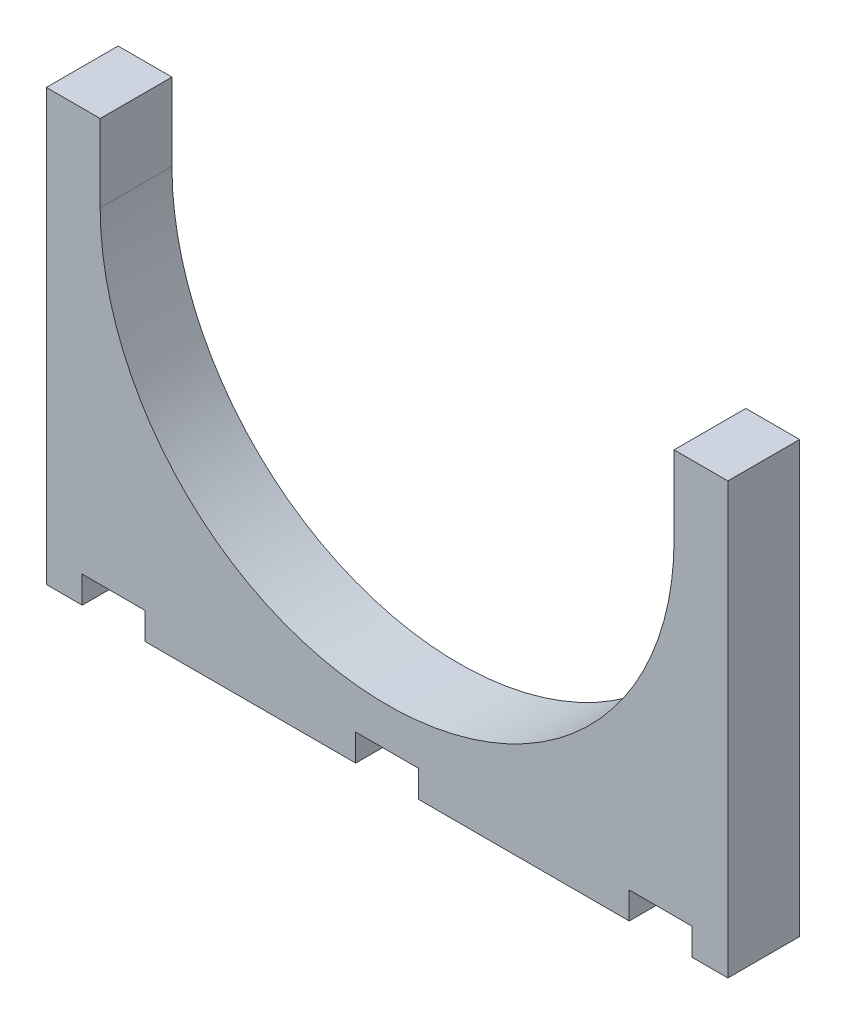
SolidWorks part; units mm, degrees
ref_plane "Front Plane" through (0, 0, 0) normal (0, 0, 1) x (1, 0, 0)
ref_plane "Top Plane" through (0, 0, 0) normal (0, 1, 0) x (1, 0, 0)
ref_plane "Right Plane" through (0, 0, 0) normal (1, 0, 0) x (0, 0, -1)
sketch "Sketch1" plane through (0, 0, 0) normal (0, 0, 1) x (1, 0, 0)
  line L0 (76.2, 500) -> (76.2, 609.6)
  line L1 (0, 0) -> (50.8, 0)
  line L2 (0, 0) -> (0, 609.6)
  line L3 (0, 609.6) -> (76.2, 609.6)
  line L4 (965.1, 0) -> (965.1, 609.6)
  line L5 (888.9, 609.6) -> (965.1, 609.6)
  line L6 (888.9, 500) -> (888.9, 609.6)
  line L7 (50.8, 0) -> (50.8, 38.1)
  line L8 (50.8, 38.1) -> (139.7, 38.1)
  line L9 (139.7, 38.1) -> (139.7, 0)
  line L10 (438.1, 0) -> (438.1, 38.1)
  line L11 (438.1, 38.1) -> (527, 38.1)
  line L12 (527, 38.1) -> (527, 0)
  line L13 (825.4, 0) -> (825.4, 38.1)
  line L14 (825.4, 38.1) -> (914.3, 38.1)
  line L15 (914.3, 38.1) -> (914.3, 0)
  line L16 (139.7, 0) -> (438.1, 0)
  line L17 (527, 0) -> (825.4, 0)
  line L18 (914.3, 0) -> (965.1, 0)
  arc A0 (76.2, 500) -> (888.9, 500) centre (482.55, 500) ccw
  dimension "D1" = 50.8
  dimension "D2" = 88.9
  dimension "D3" = 298.4
  dimension "D4" = 88.9
  dimension "D5" = 298.4
  dimension "D6" = 88.9
  dimension "D7" = 500
extrude "Boss-Extrude1" add sketch "Sketch1" along normal blind 101.6
